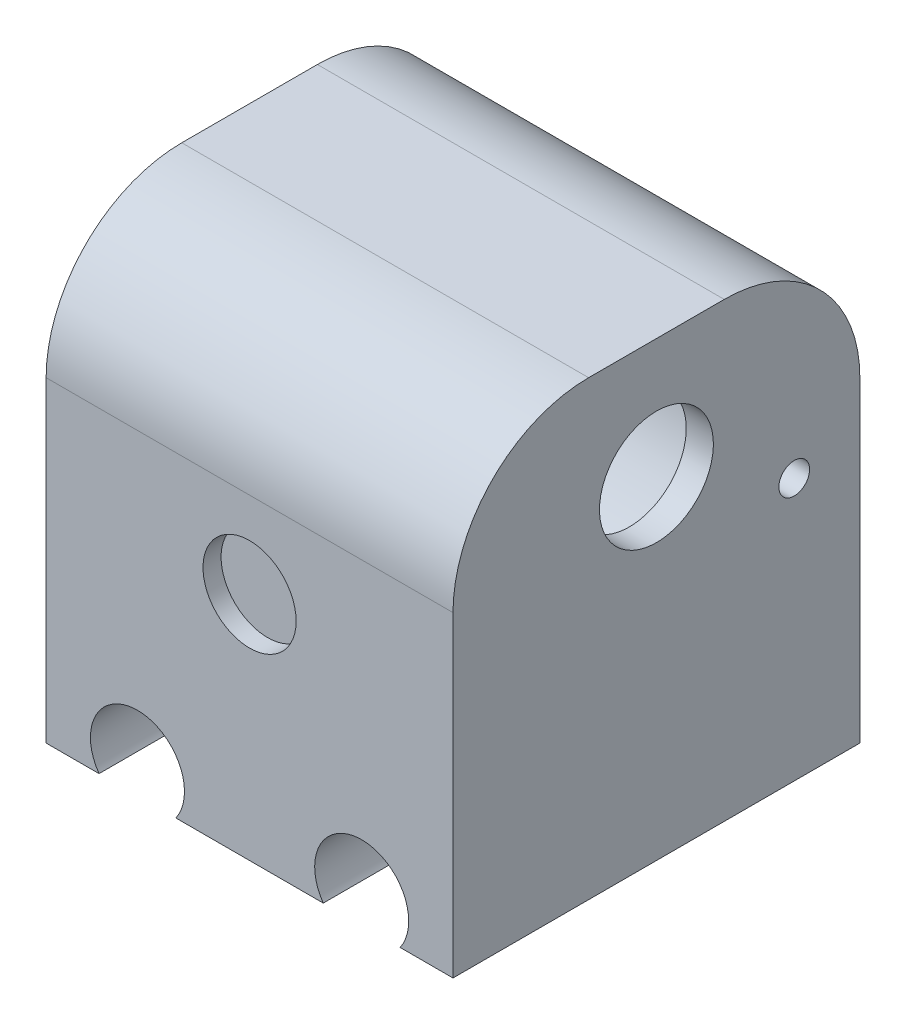
SolidWorks part; units mm, degrees
ref_plane "Front Plane" through (0, 0, 0) normal (0, 0, 1) x (1, 0, 0)
ref_plane "Top Plane" through (0, 0, 0) normal (0, 1, 0) x (1, 0, 0)
ref_plane "Right Plane" through (0, 0, 0) normal (1, 0, 0) x (0, 0, -1)
sketch "Sketch1" plane through (0, 0, 0) normal (0, 0, 1) x (1, 0, 0)
  line L1 (-14.2634, 22.0982) -> (30.7366, 22.0982)
  line L2 (-14.2634, 22.0982) -> (-14.2634, -27.9018)
  line L3 (-14.2634, -27.9018) -> (30.7366, -27.9018)
  line L4 (30.7366, 22.0982) -> (30.7366, -27.9018)
  dimension "D1" = 50
  dimension "D2" = 45
extrude "Boss-Extrude1" add sketch "Sketch1" along normal blind 45
sketch "Sketch2" plane through (0, 0, 45) normal (0, 0, 1) x (1, 0, 0)
  line L0 (-14.2634, -27.9018) -> (30.7366, -27.9018) construction
  line L1 (-14.2634, 22.0982) -> (-14.2634, -27.9018) construction
  circle A0 centre (-4.1634, -24.9018) radius 5.2
  circle A1 centre (20.6366, -24.9018) radius 5.2
  dimension "D1" = 3
  dimension "D3" = 10.1
  dimension "D2" = 2
extrude "Cut-Extrude1" cut sketch "Sketch2" against normal blind 45
sketch "Sketch9" plane through (0, 0, 45) normal (0, 0, 1) x (1, 0, 0)
  line L0 (8.2366, 22.0982) -> (8.2366, -2.4018) construction
  line L1 (30.7366, 22.0982) -> (-14.2634, 22.0982) construction
  circle A0 centre (8.2366, -2.4018) radius 5.15
  dimension "D1" = 24.5
extrude "Cut-Extrude6" cut sketch "Sketch9" against normal blind 2
sketch "Sketch10" plane through (0, 0, 0) normal (0, 0, -1) x (-1, 0, 0)
  line L0 (-8.2366, 22.0982) -> (-8.2366, -2.4018) construction
  line L1 (-30.7366, 22.0982) -> (14.2634, 22.0982) construction
  circle A0 centre (-8.2366, -2.4018) radius 5.15
  dimension "D1" = 24.5
extrude "Cut-Extrude7" cut sketch "Sketch10" against normal blind 2
sketch "Sketch12" plane through (-14.2634, 0, 0) normal (-1, 0, 0) x (0, 0, 1)
  line L0 (22.5, 22.0982) -> (22.5, -7.2504) construction
  line L1 (45, 22.0982) -> (0, 22.0982) construction
  line L2 (0, -16.4263) -> (45, -16.4263) construction
  line L3 (0, 22.0982) -> (0, -27.9018) construction
  line L4 (45, 22.0982) -> (45, -27.9018) construction
  circle A0 centre (22.5, 1.0982) radius 18.75
  dimension "D1" = 37.5
extrude "Cut-Extrude8" cut sketch "Sketch12" against normal blind 50
sketch "Sketch13" plane through (-14.2634, 0, 0) normal (-1, 0, 0) x (0, 0, 1)
  line L0 (45, 22.0982) -> (45, -27.9018) construction
  line L1 (0, 22.0982) -> (45, 22.0982)
  line L2 (0, 22.0982) -> (0, 15.4307)
  line L3 (0, 15.4307) -> (45, 15.4307)
  line L4 (45, 22.0982) -> (45, 15.4307)
extrude "Cut-Extrude9" cut sketch "Sketch13" against normal blind 46
sketch "Sketch14" plane through (-14.2634, 0, 0) normal (-1, 0, 0) x (0, 0, 1)
  line L1 (0, 15.4307) -> (45, 15.4307)
  line L2 (0, 15.4307) -> (0, 22.0982)
  line L3 (0, 22.0982) -> (45, 22.0982)
  line L4 (45, 15.4307) -> (45, 22.0982)
  dimension "D1" = 45
extrude "Boss-Extrude2" add sketch "Sketch14" against normal blind 45
sketch "Sketch15" plane through (-14.2634, 0, 0) normal (-1, 0, 0) x (0, 0, 1)
  circle A0 centre (22.5, 1.0982) radius 18.375
extrude "Cut-Extrude10" cut sketch "Sketch15" against normal blind 45
fillet "Fillet1" radius 15 2 edges at (8.2366, 22.0982, 45) (8.2366, 22.0982, 0)
sketch "Sketch16" plane through (30.7366, 0, 0) normal (1, 0, 0) x (0, 0, -1)
  circle A1 centre (-22.5, 1.0982) radius 18.75
extrude "Boss-Extrude3" add sketch "Sketch16" against normal blind 2
sketch "Sketch18" plane through (-14.2634, 0, 0) normal (-1, 0, 0) x (0, 0, 1)
  circle A0 centre (22.5, 1.0982) radius 18.75
extrude "Cut-Extrude11" cut sketch "Sketch18" against normal blind 43
sketch "Sketch19" plane through (30.7366, 0, 0) normal (1, 0, 0) x (0, 0, -1)
  line L0 (-22.5, 19.8482) -> (-22.5, 8.8482) construction
  circle A0 centre (-22.5, 1.0982) radius 18.75 construction
  circle A1 centre (-22.5, 8.8482) radius 6.3
  dimension "D1" = 11
extrude "Cut-Extrude12" cut sketch "Sketch19" against normal blind 43
sketch "Sketch20" plane through (30.7366, 0, 0) normal (1, 0, 0) x (0, 0, -1)
  circle A2 centre (-22.5, 1.0982) radius 18.75 construction
  circle A3 centre (-22.5, 1.0982) radius 16.45 construction
  circle A4 centre (-6.05, 1.0982) radius 1.7
extrude "Cut-Extrude13" cut sketch "Sketch20" against normal blind 43
sketch "Sketch21" plane through (30.7366, 0, 0) normal (1, 0, 0) x (0, 0, -1)
  circle A0 centre (-22.5, 1.0982) radius 18.75
  circle A1 centre (-22.5, 1.0982) radius 20
extrude "Boss-Extrude4" add sketch "Sketch21" along normal blind 7
sketch "Sketch22" plane through (30.7366, 0, 0) normal (1, 0, 0) x (0, 0, -1)
  circle A0 centre (-6.05, 1.0982) radius 1.7 construction
  circle A1 centre (-22.5, 8.8482) radius 6.3 construction
  circle A2 centre (-22.5, 1.0982) radius 18.75 construction
  circle A3 centre (-6.05, 1.0982) radius 1.7
  circle A4 centre (-22.5, 8.8482) radius 6.3
  circle A5 centre (-22.5, 1.0982) radius 18.75
extrude "Boss-Extrude5" add sketch "Sketch22" along normal blind 7
sketch "Sketch23" plane through (28.7366, 0, 0) normal (-1, 0, 0) x (0, 0, 1)
  circle A0 centre (22.5, 1.0982) radius 18.75 construction
  circle A1 centre (6.05, 1.0982) radius 1.7 construction
  circle A2 centre (22.5, 8.8482) radius 6.3 construction
  circle A3 centre (22.5, 1.0982) radius 18.75
  circle A4 centre (6.05, 1.0982) radius 1.7
  circle A5 centre (22.5, 8.8482) radius 6.3
extrude "Cut-Extrude14" cut sketch "Sketch23" against normal blind 7
sketch "Sketch24" plane through (37.7366, 0, 0) normal (1, 0, 0) x (0, 0, -1)
  circle A0 centre (-7.2588, 1.0982) radius 1.7
extrude "Cut-Extrude15" cut sketch "Sketch24" against normal blind 5
sketch "Sketch25" plane through (37.7366, 0, 0) normal (1, 0, 0) x (0, 0, -1)
  circle A0 centre (-7.2588, 1.0982) radius 1.7
  arc A1 (-6.6544, -0.4907) -> (-6.6544, 2.6871) centre (-6.05, 1.0982) ccw construction
  arc A2 (-6.6544, -0.4907) -> (-6.6544, 2.6871) centre (-6.05, 1.0982) ccw
  arc A3 (-6.6544, 2.6871) -> (-6.6544, -0.4907) centre (-7.2588, 1.0982) cw
  arc M3 (-6.6544, 2.6871) -> (-6.6544, -0.4907) centre (-6.05, 1.0982) cw
extrude "Boss-Extrude6" add sketch "Sketch25" against normal blind 2 contours A0 M3
sketch "Sketch26" plane through (37.7366, 0, 0) normal (1, 0, 0) x (0, 0, -1)
  circle A0 centre (-22.5, 1.0982) radius 20
  circle A1 centre (-22.5, 8.8482) radius 6.3
  circle A2 centre (-7.2588, 1.0982) radius 1.7
extrude "Boss-Extrude7" add sketch "Sketch26" against normal blind 10
sketch "Sketch27" plane through (37.7366, 0, 0) normal (1, 0, 0) x (0, 0, -1)
  circle A0 centre (-22.5, 1.0982) radius 20
extrude "Cut-Extrude16" cut sketch "Sketch27" against normal blind 7
